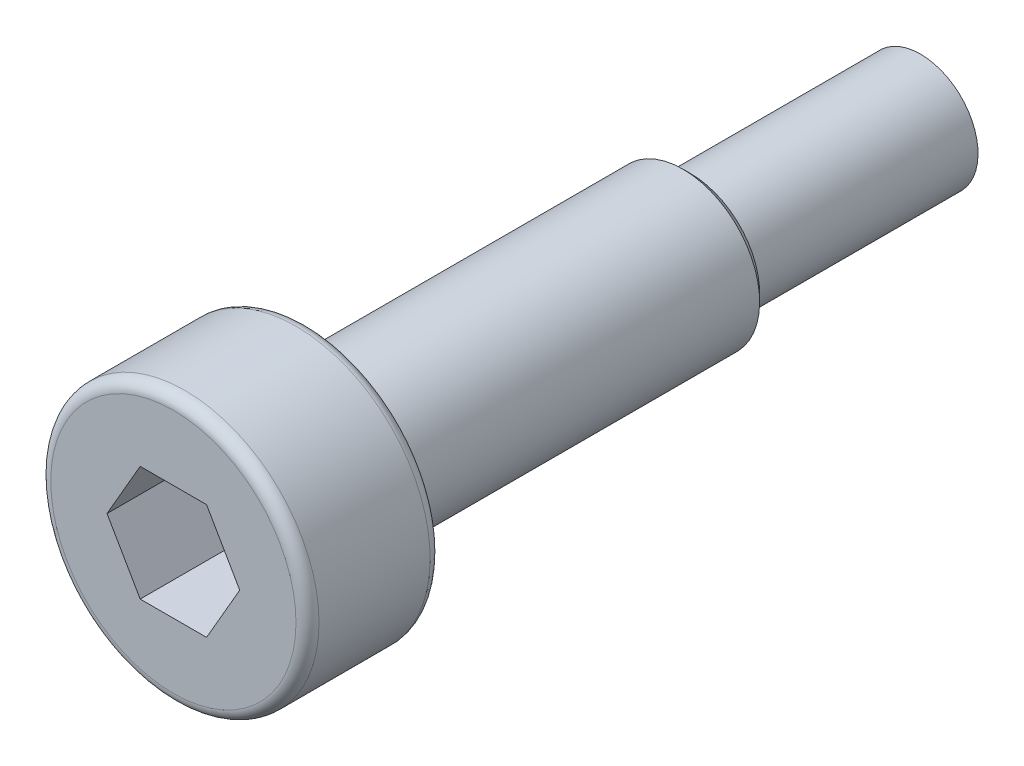
SolidWorks part; units mm, degrees
ref_plane "前视基准面" through (0, 0, 0) normal (0, 0, 1) x (1, 0, 0)
ref_plane "上视基准面" through (0, 0, 0) normal (0, 1, 0) x (1, 0, 0)
ref_plane "右视基准面" through (0, 0, 0) normal (1, 0, 0) x (0, 0, -1)
other "Configuration Table"
sketch "草图1" plane through (0, 0, 0) normal (1, 0, 0) x (0, 0, -1)
  line L0 (0, 0) -> (-19.5, 0) construction
  line L1 (0, 0) -> (0, 1.5)
  line L2 (0, 1.5) -> (-6, 1.5)
  line L3 (-6, 1.5) -> (-6, 2)
  line L4 (-6, 2) -> (-16, 2)
  line L5 (-16, 2) -> (-16, 3.5)
  line L6 (-16, 3.5) -> (-19.5, 3.5)
  line L7 (-19.5, 3.5) -> (-19.5, 0)
  line L8 (0, 0) -> (-19.5, 0)
  dimension "D1" = 3
  dimension "D2" = 4
  dimension "D3" = 6
  dimension "D4" = 7
  dimension "D5" = 3.5
  dimension "D6" = 10
revolve "旋转1" add sketch "草图1" angle 360 about L0
cosmetic thread "装饰螺纹线1" parameters "D2"=2.459
fillet "圆角1" radius 0.3 2 edges at (0, 3.5, 16) (0, 3.5, 19.5)
sketch "草图2" plane through (0, 0, 19.5) normal (0, 0, 1) x (1, 0, 0)
  line L1 (1.7321, 0) -> (0.866, 1.5)
  line L2 (0.866, 1.5) -> (-0.866, 1.5)
  line L3 (-0.866, 1.5) -> (-1.7321, 0)
  line L4 (-1.7321, 0) -> (-0.866, -1.5)
  line L5 (-0.866, -1.5) -> (0.866, -1.5)
  line L6 (0.866, -1.5) -> (1.7321, 0)
  circle A0 centre (0, 0) radius 1.5 construction
  dimension "D1" = 3
extrude "切除-拉伸1" cut sketch "草图2" against normal blind 2.4
chamfer "倒角1" distance 0.2 angle 45 1 edges at (0, 2, 6)
